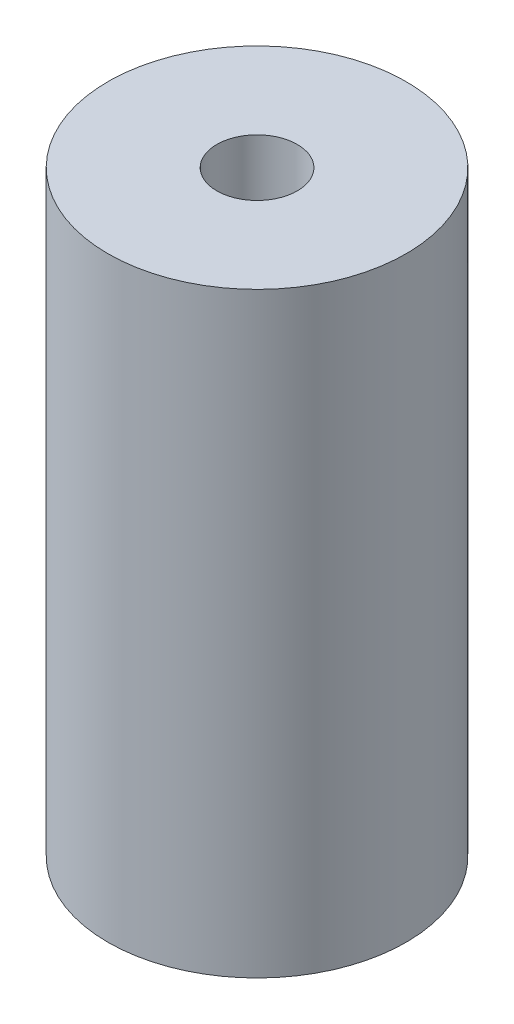
SolidWorks part; units mm, degrees
ref_plane "Front Plane" through (0, 0, 0) normal (0, 0, 1) x (1, 0, 0)
ref_plane "Top Plane" through (0, 0, 0) normal (0, 1, 0) x (1, 0, 0)
ref_plane "Right Plane" through (0, 0, 0) normal (1, 0, 0) x (0, 0, -1)
sketch "Sketch1" plane through (0, 0, 0) normal (0, 1, 0) x (1, 0, 0)
  circle A0 centre (0, 0) radius 5
extrude "Boss-Extrude1" add sketch "Sketch1" along normal blind 20
sketch "Sketch2" plane through (0, 20, 0) normal (0, 1, 0) x (1, 0, 0)
  circle A0 centre (0, 0) radius 1.35
extrude "Cut-Extrude1" cut sketch "Sketch2" against normal blind 6
sketch "Sketch12" plane through (0, 0, 0) normal (0, -1, 0) x (1, 0, 0)
  circle A0 centre (0, 0) radius 1.35
extrude "Cut-Extrude2" cut sketch "Sketch12" against normal blind 10
